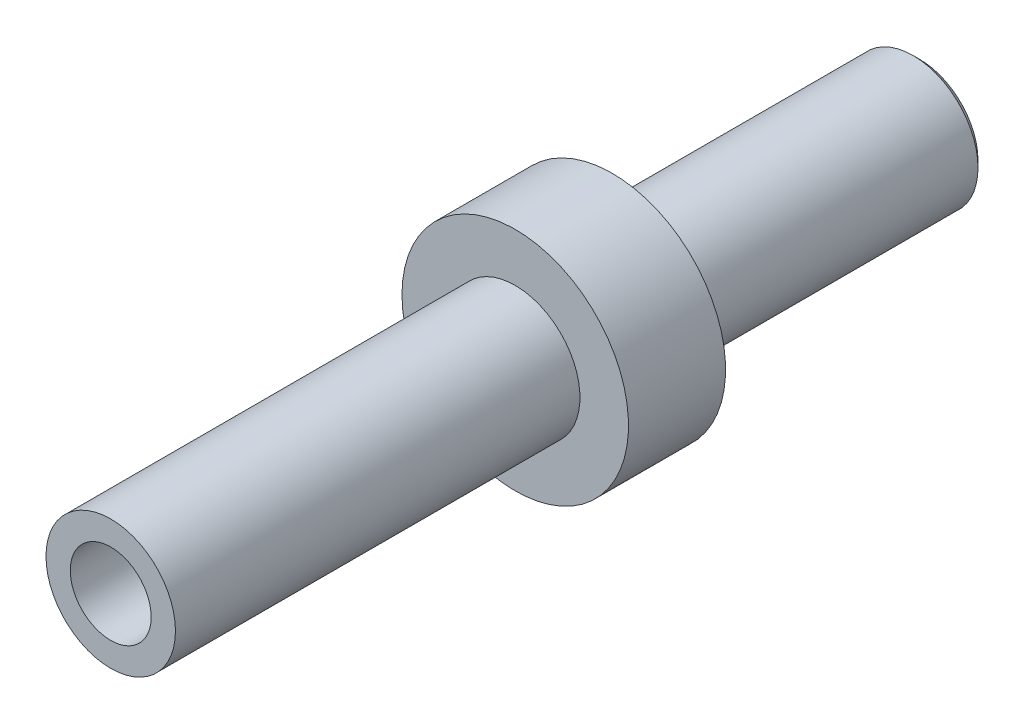
SolidWorks part; units mm, degrees
material "Латунь"
ref_plane "Спереди" through (0, 0, 0) normal (0, 0, 1) x (1, 0, 0)
ref_plane "Сверху" through (0, 0, 0) normal (0, 1, 0) x (1, 0, 0)
ref_plane "Справа" through (0, 0, 0) normal (1, 0, 0) x (0, 0, -1)
sketch "Эскиз1" plane through (0, 0, 0) normal (0, 0, 1) x (1, 0, 0)
  circle A0 centre (0, 0) radius 2
  dimension "D2" = 4
extrude "Бобышка-Вытянуть1" add sketch "Эскиз1" along normal blind 25
cosmetic thread "Условное изображение резьбы3" parameters "D1"=12.5, "D2"=3.22
sketch "Эскиз2" plane through (0, 0, 25) normal (0, 0, 1) x (1, 0, 0)
  circle A0 centre (0, 0) radius 1.25
  dimension "D1" = 2.5
extrude "Вырез-Вытянуть1" cut sketch "Эскиз2" against normal through all
sketch "Эскиз3" plane through (0, 0, 0) normal (0, 0, -1) x (-1, 0, 0)
  circle A0 centre (0, 0) radius 3.5
  circle A1 centre (0, 0) radius 2
  circle A2 centre (0, 0) radius 2 construction
  dimension "D1" = 7
extrude "Бобышка-Вытянуть2" add sketch "Эскиз3" against normal blind 3 from offset 9.5 offset against normal yes
chamfer "Фаска1" distance 0.2 angle 45 1 edges at (2, 0, 0)
